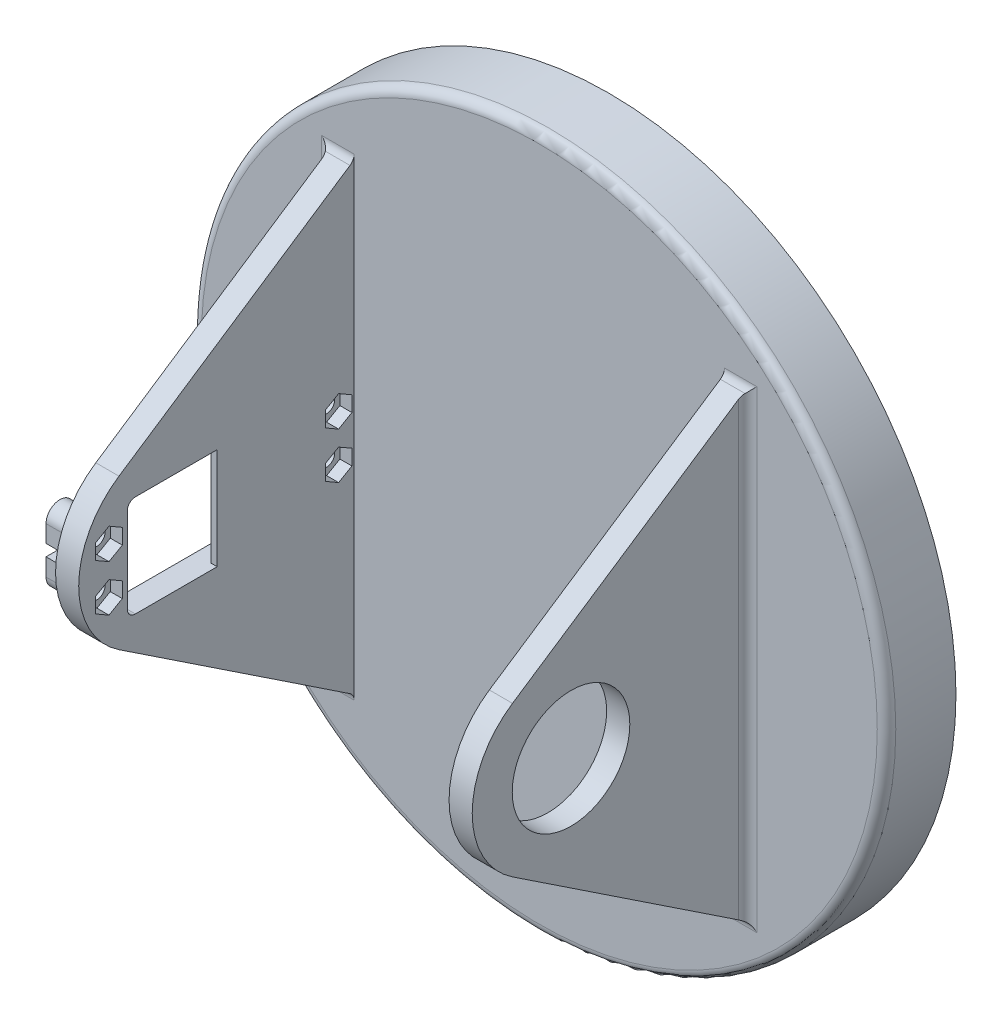
SolidWorks part; units mm, degrees
ref_plane "Front Plane" through (0, 0, 0) normal (0, 0, 1) x (1, 0, 0)
ref_plane "Top Plane" through (0, 0, 0) normal (0, 1, 0) x (1, 0, 0)
ref_plane "Right Plane" through (0, 0, 0) normal (1, 0, 0) x (0, 0, -1)
sketch "Sketch1" plane through (0, 0, 0) normal (0, 0, 1) x (1, 0, 0)
  circle A0 centre (0, 0) radius 75
  dimension "D1" = 150
extrude "Base Plate\\" add sketch "Sketch1" along normal blind 15
sketch "Sketch2" plane through (0, 0, 0) normal (0, 0, -1) x (-1, 0, 0)
  circle A0 centre (0, 0) radius 25 construction
  circle A1 centre (0, -25) radius 4.5
  circle A2 centre (-23.7764, -7.7254) radius 4.5
  circle A3 centre (-14.6946, 20.2254) radius 4.5
  circle A4 centre (14.6946, 20.2254) radius 4.5
  circle A5 centre (23.7764, -7.7254) radius 4.5
  point P16 (0, 0)
  dimension "D2" = 9
  dimension "D3" = 50
  dimension "D1" = 5
extrude "Drive Holes" cut sketch "Sketch2" against normal blind 10
chamfer "Chamfer1" distance 1 5 edges at (19.2764, -7.7254, 0) (10.1946, 20.2254, 0) (-19.1946, 20.2254, 0) (-28.2764, -7.7254, 0) (-4.5, -25, 0)
sketch "Sketch4" plane through (0, 0, 0) normal (1, 0, 0) x (0, 0, -1)
  line L0 (-15, 50) -> (-65.792, 16.2334)
  line L1 (-15, 75) -> (-15, -75) construction
  line L2 (-65.792, -16.2334) -> (-15, -50)
  line L3 (-15, -50) -> (-15, 50)
  arc A0 (-65.792, 16.2334) -> (-65.792, -16.2334) centre (-55, 0) ccw
  dimension "D1" = 100
  dimension "D2" = 40
extrude "Base Fin" add sketch "Sketch4" against normal blind 5 from offset 45
sketch "Sketch5" plane through (40, 0, 0) normal (-1, 0, 0) x (0, 0, 1)
  line L0 (15, 50) -> (15, -50)
  line L1 (15, -50) -> (65.792, -16.2334)
  line L2 (65.792, 16.2334) -> (15, 50)
  arc A0 (65.792, -16.2334) -> (65.792, 16.2334) centre (55, 0) ccw
extrude "Base Fin 2" add sketch "Sketch5" against normal blind 5 from offset 85
sketch "Sketch6" plane through (-45, 0, 0) normal (-1, 0, 0) x (0, 0, 1)
  line L0 (64, 8.8324) -> (64, -9.5676)
  line L1 (62.25, -11.3176) -> (24.05, -11.3176)
  line L2 (22.3, -9.5676) -> (22.3, 8.8324)
  line L3 (24.05, 10.5824) -> (62.25, 10.5824)
  arc A0 (64, -9.5676) -> (62.25, -11.3176) centre (62.25, -9.5676) cw
  arc A1 (24.05, -11.3176) -> (22.3, -9.5676) centre (24.05, -9.5676) cw
  arc A2 (22.3, 8.8324) -> (24.05, 10.5824) centre (24.05, 8.8324) cw
  arc A3 (62.25, 10.5824) -> (64, 8.8324) centre (62.25, 8.8324) cw
extrude "Cut-Extrude1" cut sketch "Sketch6" against normal up to next
sketch "Sketch7" plane through (-45, 0, 0) normal (-1, 0, 0) x (0, 0, 1)
  circle A0 centre (18.35, 4.6324) radius 1.75
  circle A1 centre (18.35, -5.3676) radius 1.75
  circle A2 centre (67.95, -5.3676) radius 1.75
  circle A3 centre (67.95, 4.6324) radius 1.75
  dimension "D1" = 3.5
extrude "Cut-Extrude2" cut sketch "Sketch7" against normal up to next
sketch "Sketch8" plane through (-45, 0, 0) normal (-1, 0, 0) x (0, 0, 1)
  line L0 (67.95, 4.6324) -> (67.95, -5.3676) construction
  line L1 (70.95, 4.6324) -> (70.95, -5.3676)
  line L2 (64.95, 4.6324) -> (64.95, -5.3676)
  line L3 (15, 7.6324) -> (15, 0)
  line L4 (15, -75) -> (15, 75) construction
  line L5 (15, 0) -> (15, -8.3676)
  line L6 (15, -8.3676) -> (18.35, -8.3676)
  line L7 (21.35, -5.3676) -> (21.35, 4.6324)
  line L8 (18.35, 7.6324) -> (15, 7.6324)
  arc A0 (70.95, 4.6324) -> (64.95, 4.6324) centre (67.95, 4.6324) ccw
  arc A1 (64.95, -5.3676) -> (70.95, -5.3676) centre (67.95, -5.3676) ccw
  arc A2 (18.35, -8.3676) -> (21.35, -5.3676) centre (18.35, -5.3676) ccw
  arc A3 (21.35, 4.6324) -> (18.35, 7.6324) centre (18.35, 4.6324) ccw
  circle A4 centre (18.35, 4.6324) radius 1.75 construction
  circle A5 centre (18.35, -5.3676) radius 1.75 construction
  point P4 (67.95, -0.3676)
  dimension "D1" = 3
  dimension "D2" = 3
extrude "Boss-Extrude1" add sketch "Sketch8" along normal up to surface (5.6 mm away)
sketch "Sketch9" plane through (-45, 0, 0) normal (1, 0, 0) x (0, 0, -1)
  circle A0 centre (-67.95, -5.3676) radius 1.75
  circle A1 centre (-67.95, 4.6324) radius 1.75
  circle A2 centre (-18.35, -5.3676) radius 1.75
  circle A3 centre (-18.35, 4.6324) radius 1.75
extrude "Cut-Extrude3" cut sketch "Sketch9" against normal up to surface (5.6 mm away) up to face at (-50.6, -0.3676, 18.4404)
sketch "Sketch10" plane through (-50.6, 0, 0) normal (-1, 0, 0) x (0, 0, 1)
  line L0 (21.35, 0.8824) -> (16.75, 0.8824)
  line L1 (21.35, 4.6324) -> (21.35, -5.3676) construction
  line L2 (16.75, 0.8824) -> (16.75, -1.6176)
  line L3 (16.75, -1.6176) -> (21.35, -1.6176)
  line L4 (23.05, 0.3824) -> (17.25, 0.3824) construction
  line L5 (17.25, -1.1176) -> (23.05, -1.1176) construction
  line L6 (17.25, 0.3824) -> (17.25, -1.1176) construction
  line L7 (21.35, 0.8824) -> (21.35, -1.6176)
  line L10 (64.95, -5.3676) -> (64.95, 4.6324) construction
  line L14 (64.95, -1.5747) -> (64.95, 0.9253)
  line L22 (64.95, 0.9253) -> (70.95, 0.9253)
  line L23 (70.95, 4.6324) -> (70.95, -5.3676) construction
  line L24 (70.95, 0.9253) -> (70.95, -1.5747)
  line L25 (70.95, -1.5747) -> (64.95, -1.5747)
  dimension "D1" = 0.5
  dimension "D2" = 0.5
  dimension "D3" = 0.5
extrude "Cut-Extrude4" cut sketch "Sketch10" against normal up to surface (5.6 mm away) up to face at (-45, -0.2206, 28.0928)
sketch "Sketch11" plane through (-40, 0, 0) normal (1, 0, 0) x (0, 0, -1)
  line L1 (-65.075, -7.0275) -> (-65.075, -3.7077)
  line L2 (-65.075, -3.7077) -> (-67.95, -2.0478)
  line L3 (-67.95, -2.0478) -> (-70.825, -3.7077)
  line L4 (-70.825, -3.7077) -> (-70.825, -7.0275)
  line L5 (-70.825, -7.0275) -> (-67.95, -8.6874)
  line L6 (-67.95, -8.6874) -> (-65.075, -7.0275)
  line L7 (-65.075, 2.9725) -> (-65.075, 6.2923)
  line L8 (-65.075, 6.2923) -> (-67.95, 7.9522)
  line L9 (-67.95, 7.9522) -> (-70.825, 6.2923)
  line L10 (-70.825, 6.2923) -> (-70.825, 2.9725)
  line L11 (-70.825, 2.9725) -> (-67.95, 1.3126)
  line L12 (-67.95, 1.3126) -> (-65.075, 2.9725)
  line L13 (-15.475, -7.0275) -> (-15.475, -3.7077)
  line L14 (-15.475, -3.7077) -> (-18.35, -2.0478)
  line L15 (-18.35, -2.0478) -> (-21.225, -3.7077)
  line L16 (-21.225, -3.7077) -> (-21.225, -7.0275)
  line L17 (-21.225, -7.0275) -> (-18.35, -8.6874)
  line L18 (-18.35, -8.6874) -> (-15.475, -7.0275)
  line L19 (-15.475, 2.9725) -> (-15.475, 6.2923)
  line L20 (-15.475, 6.2923) -> (-18.35, 7.9522)
  line L21 (-18.35, 7.9522) -> (-21.225, 6.2923)
  line L22 (-21.225, 6.2923) -> (-21.225, 2.9725)
  line L23 (-21.225, 2.9725) -> (-18.35, 1.3126)
  line L24 (-18.35, 1.3126) -> (-15.475, 2.9725)
  circle A0 centre (-67.95, -5.3676) radius 2.875 construction
  circle A1 centre (-67.95, 4.6324) radius 2.875 construction
  circle A2 centre (-18.35, -5.3676) radius 2.875 construction
  circle A3 centre (-18.35, 4.6324) radius 2.875 construction
  circle A4 centre (-18.35, 4.6324) radius 1.75 construction
  dimension "D1" = 5.75
extrude "Cut-Extrude5" cut sketch "Sketch11" against normal blind 2.6
sketch "Sketch12" plane through (-40, 0, 0) normal (1, 0, 0) x (0, 0, -1)
  line L0 (-44.5721, -11.3176) -> (-44.5721, 10.5824)
  line L1 (-62.25, -11.3176) -> (-24.05, -11.3176) construction
  line L2 (-24.05, 10.5824) -> (-62.25, 10.5824) construction
  line L3 (-44.5721, 10.5824) -> (-24.05, 10.5824)
  line L4 (-22.3, 8.8324) -> (-22.3, -9.5676)
  line L5 (-24.05, -11.3176) -> (-44.5721, -11.3176)
  arc A0 (-24.05, 10.5824) -> (-22.3, 8.8324) centre (-24.05, 8.8324) cw
  arc A1 (-22.3, -9.5676) -> (-24.05, -11.3176) centre (-24.05, -9.5676) cw
extrude "Boss-Extrude2" add sketch "Sketch12" against normal up to surface (1.38 mm away)
fillet "Fillet1" radius 2 9 edges at (42.5, -50, 15) (42.5, 50, 15) (45, 0, 15) (-47.8, 7.6324, 15) (-47.8, -8.3676, 15) (-42.5, -50, 15) (-42.5, 50, 15) (-45, -29.1838, 15) (-45, 28.8162, 15)
fillet "Fillet2" radius 2 1 edges at (75, 0, 15)
sketch "Sketch13" plane through (40, 0, 0) normal (-1, 0, 0) x (0, 0, 1)
  circle A0 centre (53.15, -0.3676) radius 12.7
  arc A1 (53.15, 19.6324) -> (53.15, -20.3676) centre (53.15, -0.3676) ccw construction
  dimension "D1" = 25.4
extrude "Cut-Extrude6" cut sketch "Sketch13" against normal up to next
sketch "Sketch14" plane through (40, 0, 0) normal (-1, 0, 0) x (0, 0, 1)
  line L1 (15.8928, 49.4065) -> (65.792, 16.2334) construction
  line L2 (33.6357, 37.6109) -> (32.6621, -38.2582)
  line L3 (65.792, -16.2334) -> (15.8928, -49.4065) construction
  line L4 (32.6621, -38.2582) -> (65.792, -16.2334)
  line L5 (65.792, 16.2334) -> (33.6357, 37.6109)
  arc A1 (65.792, -16.2334) -> (65.792, 16.2334) centre (55, 0) ccw
extrude "Cut-Extrude7" [suppressed] cut sketch "Sketch14" against normal blind 0.5
sketch "Sketch15" plane through (0, 0, 0) normal (0, 1, 0) x (-1, 0, 0)
  line L0 (42.6672, 15) -> (42.6672, 34.6818)
  line L1 (-47, 15) -> (-40, 15) construction
  line L2 (42.6672, 34.6818) -> (62.349, 15)
  line L3 (73, 15) -> (-73, 15) construction
  line L4 (62.349, 15) -> (42.6672, 15)
  dimension "D1" = 45
extrude "Boss-Extrude3" add sketch "Sketch15" along normal mid plane 5
fillet "Fillet3" radius 2 3 edges at (-62.349, 0, 15) (-56.4745, -2.5, 15) (-56.4745, 2.5, 15)
sketch "Sketch17" plane through (0, 0, 0) normal (0, 1, 0) x (1, 0, 0)
  line L0 (-42.6672, -13) -> (-42.6672, -30.7242)
  line L1 (75, -13) -> (-75, -13) construction
  line L2 (-42.6672, -30.7242) -> (-60.3915, -13)
  line L3 (-60.3915, -13) -> (-42.6672, -13)
extrude "Boss-Extrude4" add sketch "Sketch17" along normal mid plane 5 from offset 20
sketch "Sketch18" plane through (0, 0, 0) normal (0, 1, 0) x (-1, 0, 0)
  line L0 (58.3915, 15) -> (45, 28.3915)
  line L1 (45, 28.3915) -> (45, 15)
  line L2 (40, 15) -> (47, 15) construction
  line L3 (45, 15) -> (58.3915, 15)
extrude "Boss-Extrude5" add sketch "Sketch18" along normal mid plane 5 from offset 20
fillet "Fillet4" radius 2 8 edges at (-45, 17.5, 22.6957) (-45.5858, 17.5, 15.5858) (-45, 22.5, 22.6957) (-45.5858, 22.5, 15.5858) (-45, 20, 28.3915) (-58.3915, 20, 15) (-52.6957, 17.5, 15) (-52.6957, 22.5, 15)
